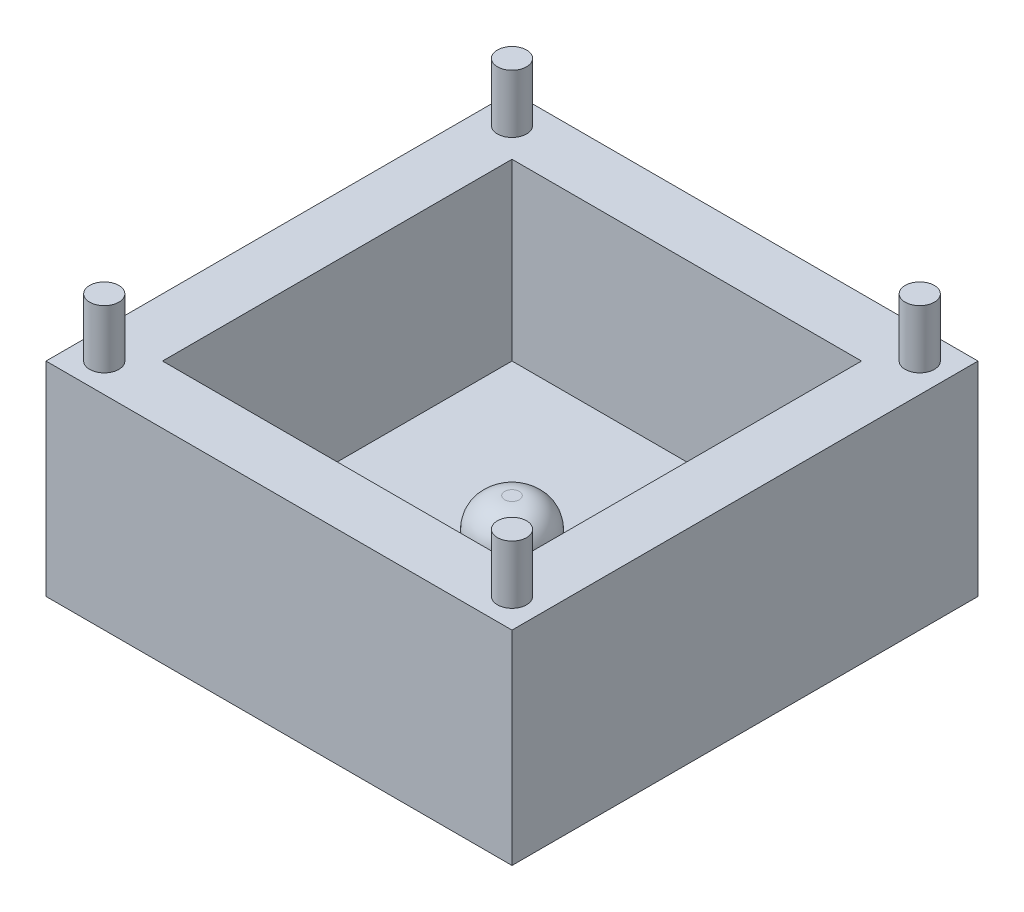
SolidWorks part; units mm, degrees
ref_plane "Front Plane" through (0, 0, 0) normal (0, 0, 1) x (1, 0, 0)
ref_plane "Top Plane" through (0, 0, 0) normal (0, 1, 0) x (1, 0, 0)
ref_plane "Right Plane" through (0, 0, 0) normal (1, 0, 0) x (0, 0, -1)
sketch "Sketch1" plane through (0, 0, 0) normal (0, 1, 0) x (1, 0, 0)
  line L1 (-8, -8) -> (8, -8)
  line L2 (-8, -8) -> (-8, 8)
  line L3 (-8, 8) -> (8, 8)
  line L4 (8, -8) -> (8, 8)
  line L5 (-8, -8) -> (8, 8) construction
  line L6 (-8, 8) -> (8, -8) construction
  point P0 (0, 0)
  dimension "D1" = 16
  dimension "D2" = 16
extrude "Boss-Extrude1" add sketch "Sketch1" along normal blind 7
sketch "Sketch2" plane through (0, 7, 0) normal (0, 1, 0) x (1, 0, 0)
  line L1 (-6, -6) -> (6, -6)
  line L2 (-6, -6) -> (-6, 6)
  line L3 (-6, 6) -> (6, 6)
  line L4 (6, -6) -> (6, 6)
  line L5 (-6, -6) -> (6, 6) construction
  line L6 (-6, 6) -> (6, -6) construction
  point P0 (0, 0)
  dimension "D1" = 12
  dimension "D2" = 12
extrude "Cut-Extrude1" cut sketch "Sketch2" against normal blind 6
sketch "Sketch3" plane through (0, 1, 0) normal (0, 1, 0) x (1, 0, 0)
  circle A0 centre (0, 0) radius 1.25
  dimension "D1" = 2.5
extrude "Boss-Extrude2" add sketch "Sketch3" along normal blind 2
fillet "Fillet1" radius 1 1 edges at (0, 3, 1.25)
sketch "Sketch4" plane through (0, 7, 0) normal (0, 1, 0) x (1, 0, 0)
  line L0 (-8, -8) -> (8, -8) construction
  line L1 (-8, 8) -> (-8, -8) construction
  line L2 (8, -8) -> (8, 8) construction
  line L3 (8, 8) -> (-8, 8) construction
  circle A0 centre (-7, 7) radius 0.5
  circle A1 centre (7, 7) radius 0.5
  circle A2 centre (7, -7) radius 0.5
  circle A3 centre (-7, -7) radius 0.5
  dimension "D1" = 1
  dimension "D4" = 1
  dimension "D5" = 1
  dimension "D7" = 1
  dimension "D10" = 1
  dimension "D2" = 1
  dimension "D3" = 1
  dimension "D6" = 1
  dimension "D8" = 1
  dimension "D9" = 1
  dimension "D11" = 1
  dimension "D12" = 1
extrude "Boss-Extrude3" add sketch "Sketch4" along normal blind 2
